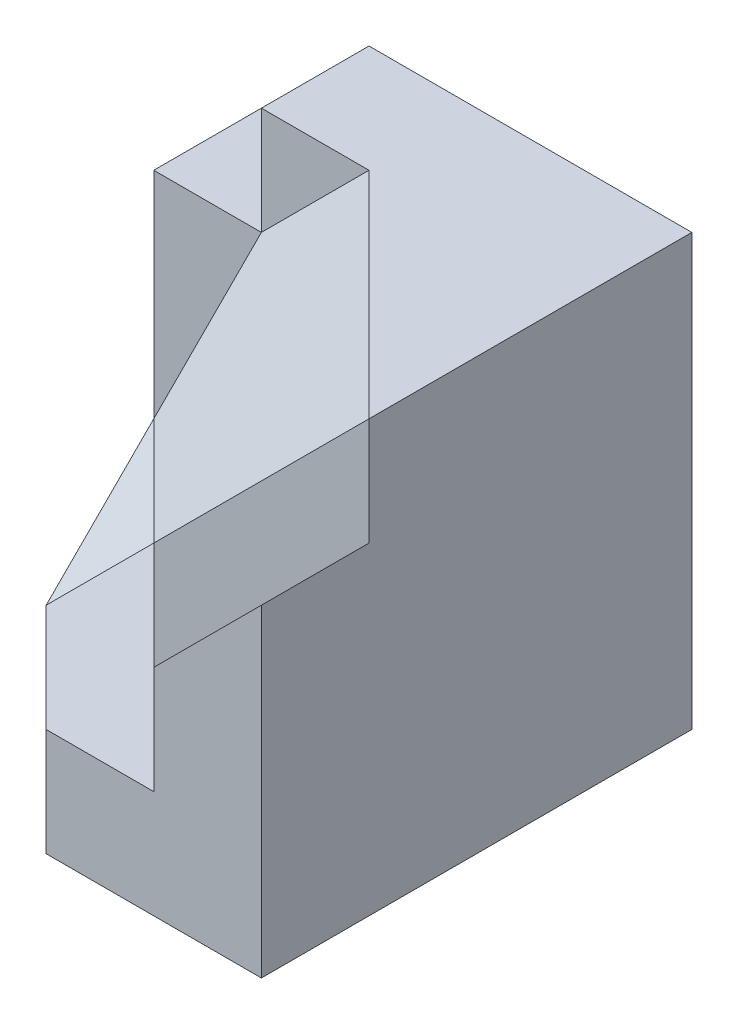
SolidWorks part; units mm, degrees
ref_plane "Front Plane" through (0, 0, 0) normal (0, 0, 1) x (1, 0, 0)
ref_plane "Top Plane" through (0, 0, 0) normal (0, 1, 0) x (1, 0, 0)
ref_plane "Right Plane" through (0, 0, 0) normal (1, 0, 0) x (0, 0, -1)
sketch "Sketch2" plane through (0, 0, 0) normal (0, 1, 0) x (1, 0, 0)
  line L0 (-15, 0) -> (0, 0)
  line L1 (0, 0) -> (0, -15)
  line L2 (0, -15) -> (-10, -5)
  line L3 (-10, -5) -> (-15, -5)
  line L4 (-15, -5) -> (-15, 0)
  dimension "D1" = 5
  dimension "D2" = 5
  dimension "D3" = 15
  dimension "D4" = 15
extrude "Boss-Extrude2" add sketch "Sketch2" along normal blind 20
sketch "Sketch3" plane through (-15, 0, 0) normal (-1, 0, 0) x (0, 0, 1)
  line L0 (5, 15) -> (5, 5)
  line L1 (0, 0) -> (10, 0)
  line L2 (0, 0) -> (0, 15)
  line L3 (0, 15) -> (5, 15)
  line L4 (5, 20) -> (5, 0) construction
  line L5 (5, 5) -> (10, 0)
  dimension "D1" = 5
  dimension "D2" = 10
  dimension "D3" = 10
  dimension "D4" = 15
extrude "Boss-Extrude4" add sketch "Sketch3" along normal blind 5
ref_plane "Plane1" through (0, 0, 0) normal (0, -1, 0) x (-1, 0, 0)
sketch "Sketch4" plane through (0, 0, 0) normal (0, -1, 0) x (-1, 0, 0)
  line L0 (15, -5) -> (10, -5)
  line L1 (10, -5) -> (0, -15)
  line L2 (0, -15) -> (10, -15)
  line L3 (10, -15) -> (15, -10)
  line L4 (15, -10) -> (15, -5)
  line L5 (20, -10) -> (15, -10) construction
  dimension "D1" = 10
  dimension "D2" = 5
extrude "Boss-Extrude6" add sketch "Sketch4" against normal blind 20 contours L3 L4 L0 L1 L2
sketch3d "3DSketch2"
  line L0 (-15, 20, 10) -> (-15, 0, 10) construction
  line L1 (-10, 20, 15) -> (-10, 0, 15) construction
  line L2 (0, 20, 0) -> (-15, 20, 0) construction
  line L3 (-15, 20, 0) -> (-15, 20, 10) construction
  line L4 (-10, 20, 15) -> (-15, 20, 10) construction
  line L5 (0, 20, 15) -> (-10, 20, 15) construction
  line L6 (-10, 20, 5) -> (0, 20, 15)
  line L7 (0, 20, 15) -> (-10, 10, 15)
  line L8 (-10, 10, 15) -> (-15, 10, 10)
  line L9 (-15, 10, 10) -> (-15, 15, 5)
  line L10 (-15, 15, 5) -> (-10, 20, 5)
  point P0 (-10, 20, 5)
  point P1 (-15, 15, 5)
  point P2 (-15, 10, 10)
  point P4 (-10, 10, 15)
  point P7 (0, 20, 15)
  dimension "D1" = 5
  dimension "D2" = 5
  dimension "D3" = 10
  dimension "D4" = 10
extrude "Cut-Extrude1" cut sketch "3DSketch2" along direction (0, -1, 0) on the side against the normal blind 20
sketch "Sketch5" plane through (0, 0, 15) normal (0, 0, 1) x (1, 0, 0)
  line L1 (0, 0) -> (-5, 0)
  line L2 (0, 0) -> (0, 15)
  line L3 (0, 15) -> (-5, 15)
  line L4 (-5, 0) -> (-5, 15)
  dimension "D1" = 15
  dimension "D2" = 5
extrude "Boss-Extrude7" add sketch "Sketch5" along normal blind 5
sketch "Sketch6" plane through (0, 0, 20) normal (0, 0, 1) x (1, 0, 0)
  line L0 (0, 15) -> (-5, 15)
  line L1 (-5, 15) -> (-5, 10)
  line L2 (-5, 15) -> (-5, 0) construction
  line L3 (-5, 10) -> (0, 15)
  dimension "D1" = 5
extrude "Cut-Extrude2" cut sketch "Sketch6" against normal blind 5
sketch "Sketch7" plane through (0, 0, 0) normal (0, -1, 0) x (-1, 0, 0)
  line L0 (15, -10) -> (10, -15)
  line L1 (10, -15) -> (5, -15)
  line L2 (5, -15) -> (5, -20)
  line L3 (5, -20) -> (10, -20)
  line L4 (10, -20) -> (15, -15)
  line L5 (15, -15) -> (15, -10)
  dimension "D1" = 5
  dimension "D2" = 5
extrude "Boss-Extrude8" add sketch "Sketch7" against normal blind 5
